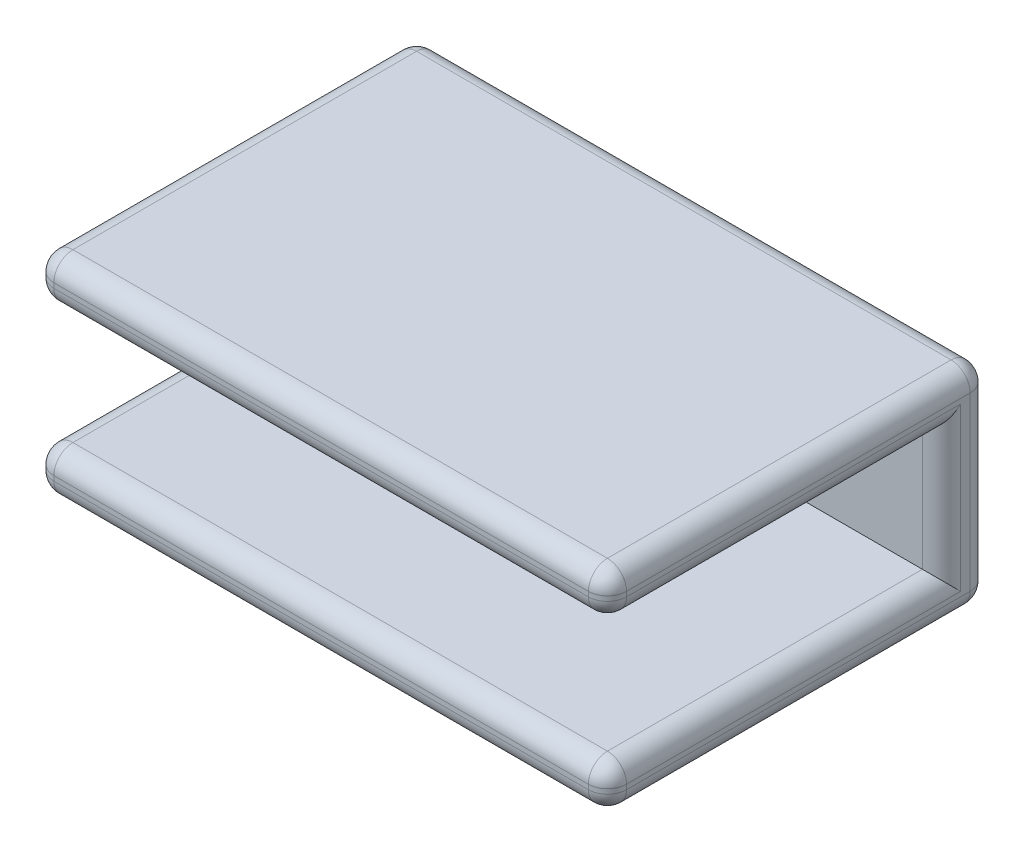
SolidWorks part; units mm, degrees
ref_plane "Front Plane" through (0, 0, 0) normal (0, 0, 1) x (1, 0, 0)
ref_plane "Top Plane" through (0, 0, 0) normal (0, 1, 0) x (1, 0, 0)
ref_plane "Right Plane" through (0, 0, 0) normal (1, 0, 0) x (0, 0, -1)
sketch "Sketch1" plane through (0, 0, 0) normal (0, 1, 0) x (1, 0, 0)
  line L1 (-15, 10) -> (15, 10)
  line L2 (-15, 10) -> (-15, -10)
  line L3 (-15, -10) -> (15, -10)
  line L4 (15, 10) -> (15, -10)
  line L5 (-15, 10) -> (15, -10) construction
  line L6 (-15, -10) -> (15, 10) construction
  point P0 (0, 0)
  dimension "D1" = 20
  dimension "D2" = 30
extrude "Boss-Extrude1" add sketch "Sketch1" along normal blind 11
sketch "Sketch2" plane through (0, 0, 10) normal (0, 0, 1) x (1, 0, 0)
  line L0 (-15, 8.75) -> (-15, 2.25)
  line L1 (-15, 8.75) -> (15, 8.75)
  line L2 (-15, 2.25) -> (15, 2.25)
  line L3 (15, 8.75) -> (15, 2.25)
  line L4 (-15, 11) -> (-15, 0) construction
  line L6 (-15, 11) -> (15, 11) construction
  line L7 (-15, 0) -> (15, 0) construction
  line L8 (15, 11) -> (15, 0) construction
  dimension "D1" = 2.25
  dimension "D2" = 2.25
extrude "Cut-Extrude1" cut sketch "Sketch2" against normal blind 17.5
fillet "Fillet1" radius 1 22 edges at (0, 11, 10) (0, 8.75, 10) (0, 0, 10) (0, 2.25, 10) (-15, 2.25, 1.25) (-15, 1.125, 10) (-15, 0, 0) (-15, 5.5, -10) (-15, 11, 0) (-15, 9.875, 10) (-15, 8.75, 1.25) (-15, 5.5, -7.5) (15, 11, 0) (15, 5.5, -10) (15, 0, 0) (15, 1.125, 10) (15, 2.25, 1.25) (15, 5.5, -7.5) (15, 8.75, 1.25) (15, 9.875, 10) (0, 0, -10) (0, 11, -10)
